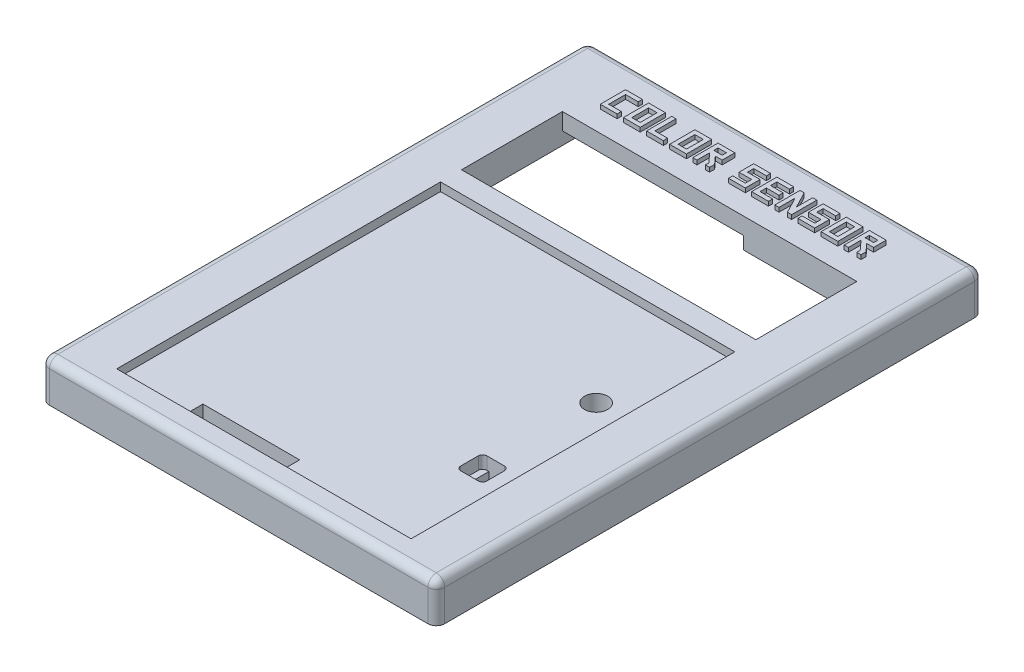
SolidWorks part; units mm, degrees
ref_plane "Front Plane" through (0, 0, 0) normal (0, 0, 1) x (1, 0, 0)
ref_plane "Top Plane" through (0, 0, 0) normal (0, 1, 0) x (1, 0, 0)
ref_plane "Right Plane" through (0, 0, 0) normal (1, 0, 0) x (0, 0, -1)
ref_plane "Plane1" through (0, 7, 0) normal (0, 1, 0) x (1, 0, 0)
sketch "Sketch1" plane through (0, 7, 0) normal (0, 1, 0) x (1, 0, 0)
  line L0 (0, 130) -> (0, 0)
  line L1 (0, 0) -> (94, 0)
  line L2 (94, 0) -> (94, 130)
  line L3 (94, 130) -> (0, 130)
extrude "Boss-Extrude1" add sketch "Sketch1" against normal blind 9.5
sketch "Sketch2" plane through (0, -2.5, 0) normal (0, -1, 0) x (1, 0, 0)
  line L0 (1.75, -128.25) -> (92.25, -128.25)
  line L1 (92.25, -128.25) -> (92.25, -1.75)
  line L2 (92.25, -1.75) -> (1.75, -1.75)
  line L3 (1.75, -1.75) -> (1.75, -128.25)
extrude "Cut-Extrude1" cut sketch "Sketch2" against normal blind 2.5
sketch "Sketch3" plane through (0, 0, 0) normal (0, -1, 0) x (1, 0, 0)
  line L0 (82, -88) -> (12, -88)
  line L1 (12, -88) -> (12, -112)
  line L2 (12, -112) -> (82, -112)
  line L3 (82, -112) -> (82, -88)
  line L7 (94, -130) -> (0, -130) construction
  point P4 (47, -112)
  point P7 (47, -130)
  dimension "D1" = 70
  dimension "D2" = 24
extrude "Cut-Extrude2" cut sketch "Sketch3" against normal through all
sketch "Sketch4" plane through (0, 7, 0) normal (0, 1, 0) x (-1, 0, 0)
  line L0 (-82, -83) -> (-12, -83)
  line L1 (-12, -83) -> (-12, -6)
  line L2 (-12, -6) -> (-82, -6)
  line L3 (-82, -6) -> (-82, -83)
  line L4 (-94, -130) -> (0, -130) construction
  line L5 (-12, -88) -> (-12, -112) construction
  point P4 (-47, -83)
  point P7 (-47, -130)
  dimension "D2" = 77
extrude "Cut-Extrude3" cut sketch "Sketch4" against normal blind 2
sketch "Sketch5" plane through (0, 5, 0) normal (0, 1, 0) x (-1, 0, 0)
  line L0 (-27.5, -7.5) -> (-50.5, -7.5)
  line L1 (-50.5, -7.5) -> (-50.5, -11)
  line L2 (-50.5, -11) -> (-27.5, -11)
  line L3 (-27.5, -11) -> (-27.5, -7.5)
  line L4 (-12, -83) -> (-12, -6) construction
  dimension "D1" = 23
  dimension "D2" = 3.5
  dimension "D3" = 15.5
extrude "Cut-Extrude4" cut sketch "Sketch5" against normal through all
sketch "Sketch6" plane through (0, 0, 0) normal (0, -1, 0) x (1, 0, 0)
  line L0 (82, -109) -> (88, -109)
  line L1 (88, -109) -> (88, -91)
  line L2 (88, -91) -> (82, -91)
  line L3 (82, -91) -> (82, -109)
  line L4 (82, -112) -> (82, -88) construction
extrude "Cut-Extrude5" cut sketch "Sketch6" against normal blind 3.5
sketch "Sketch7" plane through (0, 0, 0) normal (0, -1, 0) x (1, 0, 0)
  line L0 (12, -112) -> (12, -119.5)
  line L1 (12, -119.5) -> (55, -119.5)
  line L2 (55, -119.5) -> (55, -112)
  line L3 (55, -112) -> (12, -112)
extrude "Cut-Extrude6" cut sketch "Sketch7" against normal blind 3
fillet "Fillet1" radius 2 8 edges at (0, 2.25, 0) (0, 2.25, -130) (0, 7, -65) (94, 2.25, 0) (47, 7, 0) (47, 7, -130) (94, 7, -65) (94, 2.25, -130)
sketch "Sketch9" plane through (0, 5, 0) normal (0, 1, 0) x (1, 0, 0)
  line L1 (82, 6) -> (82, 83) construction
  line L4 (82, 83) -> (12, 83) construction
  circle A0 centre (74, 58) radius 2.75
  dimension "D1" = 5.5
  dimension "D2" = 25
  dimension "D3" = 8
extrude "Cut-Extrude7" cut sketch "Sketch9" against normal blind 5
sketch "Sketch12" plane through (0, 5, 0) normal (0, 1, 0) x (1, 0, 0)
  line L0 (82, 6) -> (82, 83) construction
  line L1 (70.9, 34.1) -> (77.1, 34.1)
  line L2 (70.9, 34.1) -> (70.9, 27.9)
  line L3 (70.9, 27.9) -> (77.1, 27.9)
  line L4 (77.1, 34.1) -> (77.1, 27.9)
  line L5 (70.9, 34.1) -> (77.1, 27.9) construction
  line L6 (70.9, 27.9) -> (77.1, 34.1) construction
  line L8 (12, 6) -> (82, 6) construction
  point P0 (74, 31)
  dimension "D1" = 6.2
  dimension "D2" = 6.2
  dimension "D3" = 8
  dimension "D4" = 25
extrude "Cut-Extrude9" cut sketch "Sketch12" against normal blind 3
sketch "Sketch13" plane through (0, 2, 0) normal (0, 1, 0) x (1, 0, 0)
  line L0 (77.1, 34.1) -> (70.9, 34.1) construction
  line L1 (70.9, 27.9) -> (77.1, 27.9) construction
  line L2 (70.9, 34.1) -> (70.9, 27.9) construction
  line L3 (77.1, 27.9) -> (77.1, 34.1) construction
  line L5 (72.4, 34.1) -> (75.6, 34.1)
  line L6 (72.4, 34.1) -> (72.4, 27.9)
  line L7 (72.4, 27.9) -> (75.6, 27.9)
  line L8 (75.6, 34.1) -> (75.6, 27.9)
  dimension "D1" = 1.5
  dimension "D2" = 1.5
extrude "Cut-Extrude10" cut sketch "Sketch13" against normal through all and the other way through all
fillet "Fillet2" radius 1 4 edges at (77.1, 3.5, -27.9) (70.9, 3.5, -27.9) (77.1, 3.5, -34.1) (70.9, 3.5, -34.1)
sketch "Sketch14" plane through (0, 0, 0) normal (0, -1, 0) x (1, 0, 0)
  circle A0 centre (74, -58) radius 4
  dimension "D1" = 8
extrude "Boss-Extrude2" add sketch "Sketch14" along normal blind 3
sketch "Sketch15" plane through (0, 0, 0) normal (0, 1, 0) x (1, 0, 0)
  circle A0 centre (74, 58) radius 2.8
  dimension "D1" = 5.6
extrude "Cut-Extrude11" cut sketch "Sketch15" against normal blind 1.5
sketch "Sketch16" plane through (0, -1.5, 0) normal (0, 1, 0) x (1, 0, 0)
  circle A2 centre (74, 58) radius 2.4
  circle A3 centre (74, 58) radius 2.4
  dimension "D1" = 0.4
extrude "Cut-Extrude12" cut sketch "Sketch16" against normal blind 1.5
sketch "Sketch18" plane through (0, 7, 0) normal (0, 1, 0) x (1, 0, 0)
  line L0 (17, 122) -> (17, 118)
  line L5 (92, 128) -> (2, 128) construction
  line L7 (17, 118) -> (19, 118)
  line L10 (15.9933, 123) -> (19.9933, 123)
  line L11 (15.9933, 123) -> (15.9933, 117)
  line L12 (15.9933, 117) -> (19.9933, 117)
  line L13 (19.9933, 123) -> (19.9933, 122)
  line L18 (17, 122) -> (19, 122)
  line L19 (19, 122) -> (19.9933, 122)
  line L20 (19, 118) -> (19.9933, 118)
  line L21 (19.9933, 118) -> (19.9933, 117)
  line L22 (66.9933, 122) -> (63.9933, 122)
  line L23 (22.4933, 122) -> (22.4933, 118)
  line L24 (62.9933, 123) -> (66.9933, 123)
  line L25 (21.4933, 123) -> (25.4933, 123)
  line L26 (21.4933, 123) -> (21.4933, 117)
  line L27 (21.4933, 117) -> (25.4933, 117)
  line L28 (25.4933, 123) -> (25.4933, 117)
  line L29 (22.4933, 118) -> (24.4933, 118)
  line L30 (24.4933, 122) -> (24.4933, 118)
  line L31 (22.4933, 122) -> (24.4933, 122)
  line L32 (27.9933, 122) -> (27.9933, 118)
  line L33 (26.9933, 123) -> (27.9933, 123)
  line L34 (26.9933, 123) -> (26.9933, 117)
  line L35 (26.9933, 117) -> (30.9933, 117)
  line L36 (30.9933, 118) -> (30.9933, 117)
  line L37 (27.9933, 118) -> (29.1094, 118)
  line L40 (27.9933, 122) -> (27.9933, 123)
  line L41 (29.1094, 118) -> (30.9933, 118)
  line L42 (33.4933, 122) -> (33.4933, 118)
  line L43 (62.9933, 123) -> (62.9933, 119.5)
  line L44 (62.9933, 117) -> (66.9933, 117)
  line L45 (66.9933, 123) -> (66.9933, 122)
  line L47 (32.4933, 123) -> (36.4933, 123)
  line L48 (32.4933, 123) -> (32.4933, 117)
  line L49 (32.4933, 117) -> (36.4933, 117)
  line L50 (36.4933, 123) -> (36.4933, 117)
  line L51 (33.4933, 118) -> (35.4933, 118)
  line L52 (35.4933, 122) -> (35.4933, 118)
  line L53 (33.4933, 122) -> (35.4933, 122)
  line L54 (49.4933, 122) -> (50.4933, 122)
  line L55 (37.9933, 123) -> (41.9933, 123)
  line L56 (37.9933, 123) -> (37.9933, 117)
  line L57 (37.9933, 117) -> (38.9933, 117)
  line L58 (41.9933, 123) -> (41.9933, 120)
  line L59 (46.4933, 123) -> (50.4933, 123)
  line L60 (46.4933, 123) -> (46.4933, 119.5)
  line L61 (46.4933, 117) -> (50.4933, 117)
  line L62 (50.4933, 123) -> (50.4933, 122)
  line L63 (47.4933, 122) -> (49.4933, 122)
  line L64 (47.4933, 122) -> (47.4933, 120.5)
  line L65 (47.4933, 120.5) -> (49.4933, 120.5)
  line L67 (47.4933, 119.5) -> (49.4933, 119.5)
  line L69 (47.9561, 118) -> (49.4933, 118)
  line L70 (49.4933, 119.5) -> (49.4933, 118)
  line L71 (49.4933, 120.5) -> (50.4933, 120.5)
  line L72 (47.4933, 119.5) -> (46.4933, 119.5)
  line L73 (47.9561, 118) -> (46.4933, 118)
  line L74 (46.4933, 118) -> (46.4933, 117)
  line L75 (50.4933, 120.5) -> (50.4933, 117)
  line L87 (55.9933, 122) -> (52.9933, 122)
  line L104 (51.9933, 123) -> (55.9933, 123)
  line L105 (51.9933, 123) -> (51.9933, 117)
  line L106 (51.9933, 117) -> (55.9933, 117)
  line L107 (55.9933, 123) -> (55.9933, 122)
  line L108 (52.9933, 122) -> (52.9933, 120.5)
  line L109 (52.9933, 120.5) -> (55.9933, 120.5)
  line L110 (55.9933, 119.5) -> (52.9933, 119.5)
  line L111 (52.9933, 119.5) -> (52.9933, 118)
  line L112 (52.9933, 118) -> (55.9933, 118)
  line L113 (55.9933, 120.5) -> (55.9933, 119.5)
  line L114 (55.9933, 118) -> (55.9933, 117)
  line L115 (58.4933, 123) -> (60.4933, 119.1633)
  line L116 (57.4933, 123) -> (58.4933, 123)
  line L117 (57.4933, 123) -> (57.4933, 117)
  line L118 (57.4933, 117) -> (58.4933, 117)
  line L119 (61.4933, 123) -> (61.4933, 117)
  line L120 (60.4933, 119.1633) -> (60.4933, 123)
  line L121 (58.4933, 117) -> (58.4933, 120.8367)
  line L122 (58.4933, 120.8367) -> (60.4933, 117)
  line L123 (60.4933, 123) -> (61.4933, 123)
  line L124 (60.4933, 117) -> (61.4933, 117)
  line L132 (63.9933, 122) -> (63.9933, 120.5)
  line L133 (63.9933, 120.5) -> (66.9933, 120.5)
  line L134 (62.9933, 119.5) -> (65.9933, 119.5)
  line L135 (65.9933, 119.5) -> (65.9933, 118)
  line L136 (65.9933, 118) -> (62.9933, 118)
  line L137 (66.9933, 120.5) -> (66.9933, 117)
  line L138 (62.9933, 118) -> (62.9933, 117)
  line L139 (69.4933, 122) -> (69.4933, 118)
  line L140 (68.4933, 123) -> (72.4933, 123)
  line L141 (68.4933, 123) -> (68.4933, 117)
  line L142 (68.4933, 117) -> (72.4933, 117)
  line L143 (72.4933, 123) -> (72.4933, 117)
  line L144 (69.4933, 118) -> (71.4933, 118)
  line L145 (71.4933, 122) -> (71.4933, 118)
  line L146 (69.4933, 122) -> (71.4933, 122)
  line L147 (41.9933, 120) -> (40.3533, 120)
  line L150 (38.9933, 118.4425) -> (38.9933, 117)
  line L151 (40.9933, 117) -> (41.9933, 117)
  line L152 (40.3533, 120) -> (41.9933, 118.2)
  line L153 (41.9933, 118.2) -> (41.9933, 117)
  line L154 (40.9933, 117) -> (40.9933, 117.8128)
  line L155 (40.9933, 117.8128) -> (39.0005, 120)
  line L156 (38.9933, 118.4425) -> (38.9933, 120)
  line L157 (38.9933, 120) -> (39.0005, 120)
  line L158 (74.9933, 117) -> (74.9933, 120)
  line L159 (38.9933, 122) -> (40.9933, 122)
  line L160 (38.9933, 122) -> (38.9933, 121)
  line L161 (38.9933, 121) -> (40.9933, 121)
  line L162 (40.9933, 122) -> (40.9933, 121)
  line L163 (73.9933, 123) -> (77.9933, 123)
  line L164 (73.9933, 123) -> (73.9933, 117)
  line L165 (73.9933, 117) -> (74.9933, 117)
  line L166 (77.9933, 123) -> (77.9933, 120)
  line L167 (74.9933, 120) -> (75.0005, 120)
  line L168 (75.0005, 120) -> (76.9933, 117.8128)
  line L169 (76.9933, 117.8128) -> (76.9933, 117)
  line L170 (77.9933, 118.2) -> (76.3533, 120)
  line L171 (76.3533, 120) -> (77.9933, 120)
  line L172 (76.9933, 117) -> (77.9933, 117)
  line L173 (77.9933, 118.2) -> (77.9933, 117)
  line L175 (74.9933, 122) -> (76.9933, 122)
  line L176 (74.9933, 122) -> (74.9933, 121)
  line L177 (74.9933, 121) -> (76.9933, 121)
  line L178 (76.9933, 122) -> (76.9933, 121)
  point P0 (76.9933, 118.2)
  point P31 (25.8727, 123)
  point P62 (48.4933, 122)
  point P63 (48.4933, 123)
  point P64 (48.4933, 119.5)
  point P65 (48.4933, 120.5)
  point P72 (56.2285, 117)
  point P74 (56.2285, 123)
  point P142 (0, 0)
  point P143 (34.8214, 120)
  point P144 (79.488, 120)
  dimension "D4" = 4
  dimension "D5" = 4
  dimension "D6" = 4
  dimension "D7" = 1
  dimension "D8" = 1
  dimension "D9" = 4
  dimension "D10" = 1
  dimension "D11" = 4
  dimension "D12" = 1
  dimension "D13" = 6
  dimension "D14" = 1.64
  dimension "D15" = 1
  dimension "D16" = 3.5
  dimension "D17" = 2
  dimension "D18" = 1
  dimension "D19" = 4
  dimension "D20" = 1
  dimension "D21" = 1
  dimension "D22" = 1
  dimension "D23" = 1.5
  dimension "D24" = 1.5
  dimension "D25" = 1
  dimension "D26" = 1
  dimension "D27" = 4
  dimension "D28" = 1
  dimension "D29" = 1
  dimension "D30" = 1
  dimension "D31" = 1
  dimension "D32" = 1
  dimension "D33" = 1
  dimension "D34" = 1
  dimension "D35" = 1.5
  dimension "D36" = 1
  dimension "D37" = 1
  dimension "D38" = 1
  dimension "D39" = 4
  dimension "D40" = 4
  dimension "D41" = 3
  dimension "D42" = 1
  dimension "D43" = 1
  dimension "D44" = 1
  dimension "D45" = 1
  dimension "D46" = 1
  dimension "D47" = 5
  dimension "D48" = 1
  dimension "D49" = 1.2
  dimension "D50" = 4
  dimension "D51" = 3
  dimension "D52" = 1.2
  dimension "D53" = 1
  dimension "D54" = 1
  dimension "D55" = 1
  dimension "D56" = 1
  dimension "D57" = 1
  dimension "D58" = 5
  dimension "D59" = 1
  dimension "D60" = 1.5
  dimension "D61" = 6
  dimension "D62" = 1.5
  dimension "D63" = 1
  dimension "D64" = 4
  dimension "D65" = 1.5
  dimension "D66" = 1.5
  dimension "D67" = 4.5
  dimension "D68" = 1
  dimension "D69" = 2
  dimension "D70" = 1.64
  dimension "D71" = 1.5
  dimension "D72" = 1.5
  dimension "D73" = 1.5
  dimension "D74" = 1.5
  dimension "D75" = 1.5
extrude "Boss-Extrude3" add sketch "Sketch18" along normal blind 1
